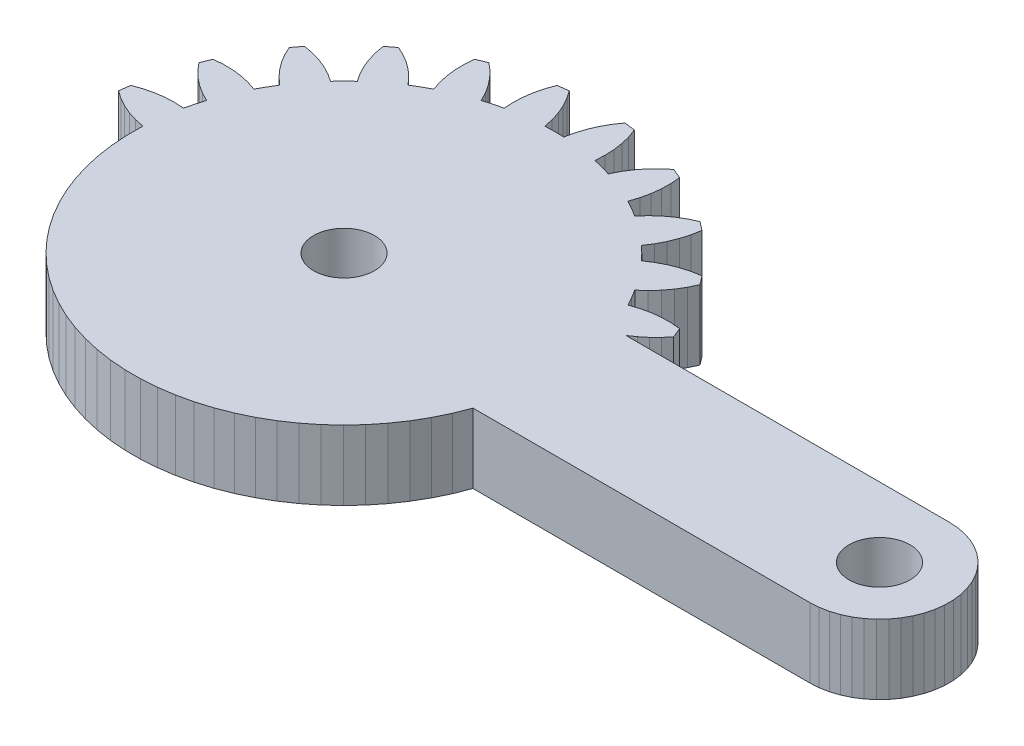
SolidWorks part; units mm, degrees
ref_plane "Front Plane" through (0, 0, 0) normal (0, 0, 1) x (1, 0, 0)
ref_plane "Top Plane" through (0, 0, 0) normal (0, 1, 0) x (1, 0, 0)
ref_plane "Right Plane" through (0, 0, 0) normal (1, 0, 0) x (0, 0, -1)
ref_plane "Plane1" through (0, 0, 0) normal (0, -1, 0) x (1, 0, 0)
sketch "Sketch1" plane through (0, 0, 0) normal (0, -1, 0) x (1, 0, 0)
  line L72 (8.6089, 1.6865) -> (8.6535, 1.1481)
  line L73 (8.6535, 1.1481) -> (9.2302, 0.9092)
  line L74 (9.2302, 0.9092) -> (9.6424, 1.2584)
  line L75 (9.6424, 1.2584) -> (10.0177, 1.647)
  line L76 (10.0177, 1.647) -> (10.3523, 2.0712)
  line L77 (10.3523, 2.0712) -> (10.6428, 2.5266)
  line L78 (10.6428, 2.5266) -> (10.8864, 3.0089)
  line L79 (10.8864, 3.0089) -> (11.4075, 2.8566)
  line L80 (11.4075, 2.8566) -> (11.9349, 2.7279)
  line L81 (11.9349, 2.7279) -> (11.9047, 2.1885)
  line L82 (11.9047, 2.1885) -> (11.9286, 1.6488)
  line L83 (11.9286, 1.6488) -> (12.0062, 1.1142)
  line L84 (12.0062, 1.1142) -> (12.137, 0.59)
  line L85 (12.137, 0.59) -> (12.3194, 0.0815)
  line L86 (12.3194, 0.0815) -> (12.9382, 0)
  line L87 (12.9382, 0) -> (13.2461, 0.444)
  line L88 (13.2461, 0.444) -> (13.508, 0.9165)
  line L89 (13.508, 0.9165) -> (13.7214, 1.4128)
  line L90 (13.7214, 1.4128) -> (13.8841, 1.9279)
  line L91 (13.8841, 1.9279) -> (13.9946, 2.4568)
  line L92 (13.9946, 2.4568) -> (14.5373, 2.4446)
  line L93 (14.5373, 2.4446) -> (15.08, 2.4568)
  line L94 (15.08, 2.4568) -> (15.1905, 1.9279)
  line L95 (15.1905, 1.9279) -> (15.3532, 1.4128)
  line L96 (15.3532, 1.4128) -> (15.5666, 0.9165)
  line L97 (15.5666, 0.9165) -> (15.8286, 0.444)
  line L98 (15.8286, 0.444) -> (16.1364, 0)
  line L99 (16.1364, 0) -> (16.7552, 0.0815)
  line L100 (16.7552, 0.0815) -> (16.9377, 0.59)
  line L101 (16.9377, 0.59) -> (17.0684, 1.1142)
  line L102 (17.0684, 1.1142) -> (17.1461, 1.6488)
  line L103 (17.1461, 1.6488) -> (17.1699, 2.1885)
  line L104 (17.1699, 2.1885) -> (17.1398, 2.7279)
  line L105 (17.1398, 2.7279) -> (17.6672, 2.8566)
  line L106 (17.6672, 2.8566) -> (18.1882, 3.0089)
  line L107 (18.1882, 3.0089) -> (18.4318, 2.5266)
  line L108 (18.4318, 2.5266) -> (18.7223, 2.0712)
  line L109 (18.7223, 2.0712) -> (19.0569, 1.647)
  line L110 (19.0569, 1.647) -> (19.4322, 1.2584)
  line L111 (19.4322, 1.2584) -> (19.8445, 0.9092)
  line L112 (19.8445, 0.9092) -> (20.4211, 1.1481)
  line L113 (20.4211, 1.1481) -> (20.4657, 1.6865)
  line L114 (20.4657, 1.6865) -> (20.4563, 2.2266)
  line L115 (20.4563, 2.2266) -> (20.393, 2.7632)
  line L116 (20.393, 2.7632) -> (20.2763, 3.2907)
  line L117 (20.2763, 3.2907) -> (20.1076, 3.8039)
  line L118 (20.1076, 3.8039) -> (20.5837, 4.0647)
  line L119 (20.5837, 4.0647) -> (21.0476, 4.3466)
  line L120 (21.0476, 4.3466) -> (21.4077, 3.9438)
  line L121 (21.4077, 3.9438) -> (21.8062, 3.5791)
  line L122 (21.8062, 3.5791) -> (22.2392, 3.256)
  line L123 (22.2392, 3.256) -> (22.7023, 2.9777)
  line L124 (22.7023, 2.9777) -> (23.1908, 2.7472)
  line L125 (23.1908, 2.7472) -> (23.686, 3.1272)
  line L126 (23.686, 3.1272) -> (23.5898, 3.6587)
  line L127 (23.5898, 3.6587) -> (23.4409, 4.1781)
  line L128 (23.4409, 4.1781) -> (23.2408, 4.6799)
  line L129 (23.2408, 4.6799) -> (22.9916, 5.1593)
  line L130 (22.9916, 5.1593) -> (22.6958, 5.6113)
  line L131 (22.6958, 5.6113) -> (23.0882, 5.9864)
  line L132 (23.0882, 5.9864) -> (23.4633, 6.3788)
  line L133 (23.4633, 6.3788) -> (23.9154, 6.083)
  line L134 (23.9154, 6.083) -> (24.3947, 5.8338)
  line L135 (24.3947, 5.8338) -> (24.8966, 5.6338)
  line L136 (24.8966, 5.6338) -> (25.4159, 5.4849)
  line L137 (25.4159, 5.4849) -> (25.9475, 5.3886)
  line L138 (25.9475, 5.3886) -> (26.3274, 5.8838)
  line L139 (26.3274, 5.8838) -> (26.0969, 6.3724)
  line L140 (26.0969, 6.3724) -> (25.8186, 6.8355)
  line L141 (25.8186, 6.8355) -> (25.4955, 7.2684)
  line L142 (25.4955, 7.2684) -> (25.1308, 7.6669)
  line L143 (25.1308, 7.6669) -> (24.728, 8.027)
  line L144 (24.728, 8.027) -> (25.0099, 8.4909)
  line L145 (25.0099, 8.4909) -> (25.2708, 8.967)
  line L146 (25.2708, 8.967) -> (25.784, 8.7983)
  line L147 (25.784, 8.7983) -> (26.3115, 8.6817)
  line L148 (26.3115, 8.6817) -> (26.848, 8.6183)
  line L149 (26.848, 8.6183) -> (27.3881, 8.6089)
  line L150 (27.3881, 8.6089) -> (27.9265, 8.6535)
  line L151 (27.9265, 8.6535) -> (28.1654, 9.2302)
  line L152 (28.1654, 9.2302) -> (27.8513, 9.6046)
  line L153 (27.8513, 9.6046) -> (27.5047, 9.9491)
  line L154 (27.5047, 9.9491) -> (27.1283, 10.2609)
  line L155 (27.1283, 10.2609) -> (26.7253, 10.5373)
  line L156 (26.7253, 10.5373) -> (45.2873, 10.5373)
  line L157 (45.2873, 10.5373) -> (45.7886, 10.5689)
  line L158 (45.7886, 10.5689) -> (46.2821, 10.663)
  line L159 (46.2821, 10.663) -> (46.7598, 10.8182)
  line L160 (46.7598, 10.8182) -> (47.2143, 11.0321)
  line L161 (47.2143, 11.0321) -> (47.6384, 11.3013)
  line L162 (47.6384, 11.3013) -> (48.0255, 11.6214)
  line L163 (48.0255, 11.6214) -> (48.3694, 11.9876)
  line L164 (48.3694, 11.9876) -> (48.6646, 12.394)
  line L165 (48.6646, 12.394) -> (48.9066, 12.8342)
  line L166 (48.9066, 12.8342) -> (49.0915, 13.3012)
  line L167 (49.0915, 13.3012) -> (49.2165, 13.7878)
  line L168 (49.2165, 13.7878) -> (49.2794, 14.2862)
  line L169 (49.2794, 14.2862) -> (49.2794, 14.7885)
  line L170 (49.2794, 14.7885) -> (49.2165, 15.2868)
  line L171 (49.2165, 15.2868) -> (49.0915, 15.7734)
  line L172 (49.0915, 15.7734) -> (48.9066, 16.2404)
  line L173 (48.9066, 16.2404) -> (48.6646, 16.6806)
  line L174 (48.6646, 16.6806) -> (48.3694, 17.087)
  line L175 (48.3694, 17.087) -> (48.0255, 17.4532)
  line L176 (48.0255, 17.4532) -> (47.6384, 17.7734)
  line L177 (47.6384, 17.7734) -> (47.2143, 18.0425)
  line L178 (47.2143, 18.0425) -> (46.7598, 18.2564)
  line L179 (46.7598, 18.2564) -> (46.2821, 18.4116)
  line L180 (46.2821, 18.4116) -> (45.7886, 18.5058)
  line L181 (45.7886, 18.5058) -> (45.2873, 18.5373)
  line L182 (45.2873, 18.5373) -> (25.9493, 18.5373)
  line L183 (25.9493, 18.5373) -> (25.6176, 19.381)
  line L184 (25.6176, 19.381) -> (25.2237, 20.1974)
  line L185 (25.2237, 20.1974) -> (24.7696, 20.9821)
  line L186 (24.7696, 20.9821) -> (24.258, 21.7305)
  line L187 (24.258, 21.7305) -> (23.6919, 22.4385)
  line L188 (23.6919, 22.4385) -> (23.0743, 23.1021)
  line L189 (23.0743, 23.1021) -> (22.4086, 23.7175)
  line L190 (22.4086, 23.7175) -> (21.6988, 24.2814)
  line L191 (21.6988, 24.2814) -> (20.9487, 24.7905)
  line L192 (20.9487, 24.7905) -> (20.1626, 25.242)
  line L193 (20.1626, 25.242) -> (19.3449, 25.6333)
  line L194 (19.3449, 25.6333) -> (18.5001, 25.9623)
  line L195 (18.5001, 25.9623) -> (17.6331, 26.2271)
  line L196 (17.6331, 26.2271) -> (16.7487, 26.4261)
  line L197 (16.7487, 26.4261) -> (15.8519, 26.5584)
  line L198 (15.8519, 26.5584) -> (14.9477, 26.6231)
  line L199 (14.9477, 26.6231) -> (14.0411, 26.6199)
  line L200 (14.0411, 26.6199) -> (13.1374, 26.5488)
  line L201 (13.1374, 26.5488) -> (12.2415, 26.4101)
  line L202 (12.2415, 26.4101) -> (11.3585, 26.2048)
  line L203 (11.3585, 26.2048) -> (10.4934, 25.9339)
  line L204 (10.4934, 25.9339) -> (9.651, 25.5989)
  line L205 (9.651, 25.5989) -> (8.8361, 25.2018)
  line L206 (8.8361, 25.2018) -> (8.0532, 24.7447)
  line L207 (8.0532, 24.7447) -> (7.3068, 24.2303)
  line L208 (7.3068, 24.2303) -> (6.6009, 23.6614)
  line L209 (6.6009, 23.6614) -> (5.9397, 23.0412)
  line L210 (5.9397, 23.0412) -> (5.3268, 22.3732)
  line L211 (5.3268, 22.3732) -> (4.7657, 21.6612)
  line L212 (4.7657, 21.6612) -> (4.2595, 20.9092)
  line L213 (4.2595, 20.9092) -> (3.811, 20.1214)
  line L214 (3.811, 20.1214) -> (3.4229, 19.3021)
  line L215 (3.4229, 19.3021) -> (3.0971, 18.4561)
  line L216 (3.0971, 18.4561) -> (2.8357, 17.5881)
  line L217 (2.8357, 17.5881) -> (2.6401, 16.7029)
  line L218 (2.6401, 16.7029) -> (2.5113, 15.8056)
  line L219 (2.5113, 15.8056) -> (2.45, 14.9011)
  line L220 (2.45, 14.9011) -> (2.4568, 13.9946)
  line L221 (2.4568, 13.9946) -> (1.9279, 13.8841)
  line L222 (1.9279, 13.8841) -> (1.4128, 13.7214)
  line L223 (1.4128, 13.7214) -> (0.9165, 13.508)
  line L224 (0.9165, 13.508) -> (0.444, 13.2461)
  line L225 (0.444, 13.2461) -> (0, 12.9382)
  line L226 (0, 12.9382) -> (0.0815, 12.3194)
  line L227 (0.0815, 12.3194) -> (0.59, 12.137)
  line L228 (0.59, 12.137) -> (1.1142, 12.0062)
  line L229 (1.1142, 12.0062) -> (1.6488, 11.9286)
  line L230 (1.6488, 11.9286) -> (2.1885, 11.9047)
  line L231 (2.1885, 11.9047) -> (2.7279, 11.9349)
  line L232 (2.7279, 11.9349) -> (2.8566, 11.4075)
  line L233 (2.8566, 11.4075) -> (3.0089, 10.8864)
  line L234 (3.0089, 10.8864) -> (2.5266, 10.6428)
  line L235 (2.5266, 10.6428) -> (2.0712, 10.3523)
  line L236 (2.0712, 10.3523) -> (1.647, 10.0177)
  line L237 (1.647, 10.0177) -> (1.2584, 9.6424)
  line L238 (1.2584, 9.6424) -> (0.9092, 9.2302)
  line L239 (0.9092, 9.2302) -> (1.1481, 8.6535)
  line L240 (1.1481, 8.6535) -> (1.6865, 8.6089)
  line L241 (1.6865, 8.6089) -> (2.2266, 8.6183)
  line L242 (2.2266, 8.6183) -> (2.7632, 8.6817)
  line L243 (2.7632, 8.6817) -> (3.2907, 8.7983)
  line L244 (3.2907, 8.7983) -> (3.8039, 8.967)
  line L245 (3.8039, 8.967) -> (4.0647, 8.4909)
  line L246 (4.0647, 8.4909) -> (4.3466, 8.027)
  line L247 (4.3466, 8.027) -> (3.9438, 7.6669)
  line L248 (3.9438, 7.6669) -> (3.5791, 7.2684)
  line L249 (3.5791, 7.2684) -> (3.256, 6.8355)
  line L250 (3.256, 6.8355) -> (2.9777, 6.3724)
  line L251 (2.9777, 6.3724) -> (2.7472, 5.8838)
  line L252 (2.7472, 5.8838) -> (3.1272, 5.3886)
  line L253 (3.1272, 5.3886) -> (3.6587, 5.4849)
  line L254 (3.6587, 5.4849) -> (4.1781, 5.6338)
  line L255 (4.1781, 5.6338) -> (4.6799, 5.8338)
  line L256 (4.6799, 5.8338) -> (5.1593, 6.083)
  line L257 (5.1593, 6.083) -> (5.6113, 6.3788)
  line L258 (5.6113, 6.3788) -> (5.9864, 5.9864)
  line L259 (5.9864, 5.9864) -> (6.3788, 5.6113)
  line L260 (6.3788, 5.6113) -> (6.083, 5.1593)
  line L261 (6.083, 5.1593) -> (5.8338, 4.6799)
  line L262 (5.8338, 4.6799) -> (5.6338, 4.1781)
  line L263 (5.6338, 4.1781) -> (5.4849, 3.6587)
  line L264 (5.4849, 3.6587) -> (5.3886, 3.1272)
  line L265 (5.3886, 3.1272) -> (5.8838, 2.7472)
  line L266 (5.8838, 2.7472) -> (6.3724, 2.9777)
  line L267 (6.3724, 2.9777) -> (6.8355, 3.256)
  line L268 (6.8355, 3.256) -> (7.2684, 3.5791)
  line L269 (7.2684, 3.5791) -> (7.6669, 3.9438)
  line L270 (7.6669, 3.9438) -> (8.027, 4.3466)
  line L271 (8.027, 4.3466) -> (8.4909, 4.0647)
  line L272 (8.4909, 4.0647) -> (8.967, 3.8039)
  line L273 (8.967, 3.8039) -> (8.7983, 3.2907)
  line L274 (8.7983, 3.2907) -> (8.6817, 2.7632)
  line L275 (8.6817, 2.7632) -> (8.6183, 2.2266)
  line L276 (8.6183, 2.2266) -> (8.6089, 1.6865)
  circle A0 centre (14.5437, 14.5356) radius 1.75
  circle A2 centre (45.2873, 14.5373) radius 1.75
extrude "Boss-Extrude1" add sketch "Sketch1" against normal blind 4
